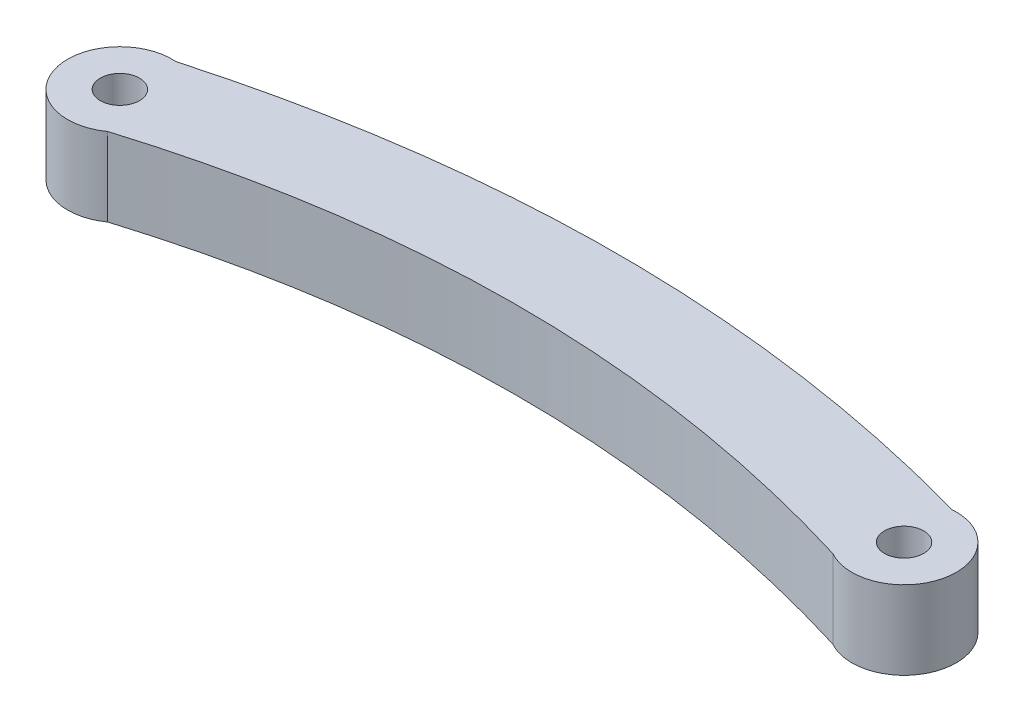
SolidWorks part; units mm, degrees
ref_plane "Front Plane" through (0, 0, 0) normal (0, 0, 1) x (1, 0, 0)
ref_plane "Top Plane" through (0, 0, 0) normal (0, 1, 0) x (1, 0, 0)
ref_plane "Right Plane" through (0, 0, 0) normal (1, 0, 0) x (0, 0, -1)
sketch "Sketch1" plane through (0, 0, 0) normal (0, 1, 0) x (1, 0, 0)
  line L0 (-60, 9.6866) -> (0, 9.6866) construction
  line L1 (0, 0) -> (-60, 0) construction
  line L2 (0, 0) -> (0, 19.3732) construction
  line L3 (0, 19.3732) -> (-60, 19.3732) construction
  line L4 (-60, 0) -> (-60, 19.3732) construction
  line L5 (-30, 19.3732) -> (-30, 0) construction
  arc A0 (-59.6876, 12.7744) -> (-57.6753, 5.5315) centre (-60, 8.7866) ccw
  arc A1 (-0.3124, 12.7744) -> (-1.9799, 5.3109) centre (0, 8.7866) cw
  circle A2 centre (-60, 8.7866) radius 1.5
  circle A3 centre (0, 8.7866) radius 1.5
  spline S0 degree 3 poles (-57.6753, 5.5315) (-48.4502, 8.3682) (-29.8851, 11.1079) (-11.3199, 8.1599) (-1.9799, 5.3109) knots 0.038745 0.038745 0.038745 0.038745 0.5 0.967002 0.967002 0.967002 0.967002
  spline S1 degree 3 poles (-59.6876, 12.7744) (-49.7918, 15.5409) (-30, 18.3075) (-10.2082, 15.5409) (-0.3124, 12.7744) knots 0.005206 0.005206 0.005206 0.005206 0.5 0.994794 0.994794 0.994794 0.994794
  dimension "D6" = 8
  dimension "D2" = 3
  dimension "D1" = 60
extrude "Boss-Extrude1" add sketch "Sketch1" along normal blind 6 contours S1 A1 S0 A0 | A2 | A3
